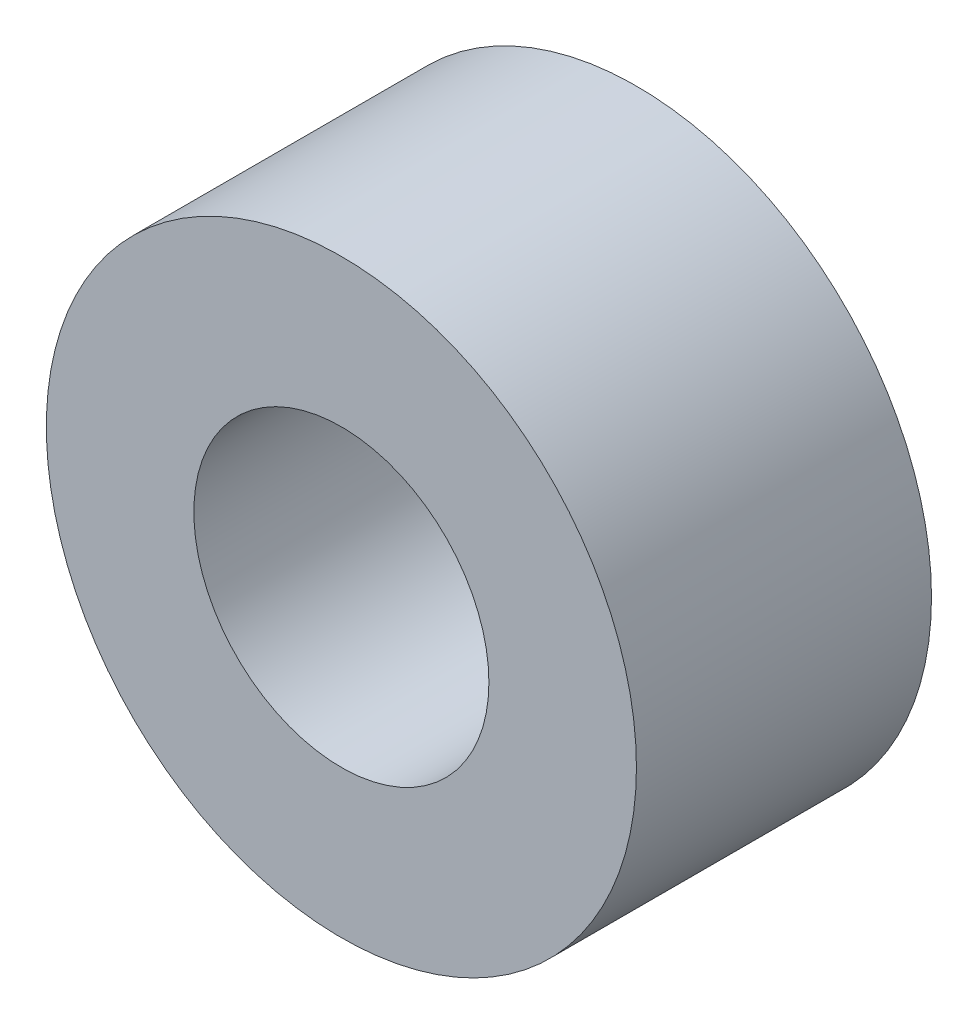
SolidWorks part; units mm, degrees
ref_plane "Plan de face" through (0, 0, 0) normal (0, 0, 1) x (1, 0, 0)
ref_plane "Plan de dessus" through (0, 0, 0) normal (0, 1, 0) x (1, 0, 0)
ref_plane "Plan de droite" through (0, 0, 0) normal (1, 0, 0) x (0, 0, -1)
sketch "Esquisse1" plane through (0, 0, 0) normal (0, 0, 1) x (1, 0, 0)
  circle A0 centre (0, 0) radius 1
  circle A1 centre (0, 0) radius 2
  dimension "D1" = 4
  dimension "D2" = 2
extrude "Boss.-Extru.1" add sketch "Esquisse1" along normal blind 2
